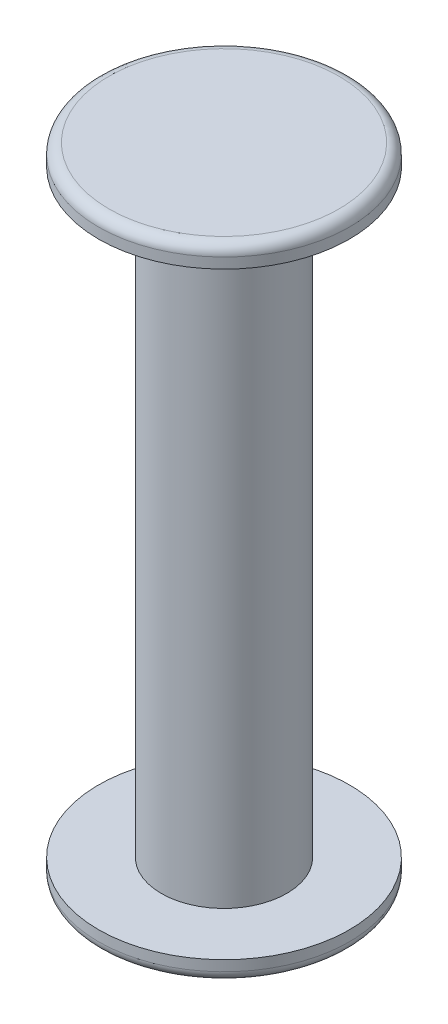
SolidWorks part; units mm, degrees
ref_plane "前视基准面" through (0, 0, 0) normal (0, 0, 1) x (1, 0, 0)
ref_plane "上视基准面" through (0, 0, 0) normal (0, 1, 0) x (1, 0, 0)
ref_plane "右视基准面" through (0, 0, 0) normal (1, 0, 0) x (0, 0, -1)
sketch "草图1" plane through (0, 0, 0) normal (0, 1, 0) x (1, 0, 0)
  circle A0 centre (0, 0) radius 3
  dimension "D1" = 6
extrude "凸台-拉伸1" add sketch "草图1" along normal mid plane 28.6
sketch "草图2" plane through (0, 14.3, 0) normal (0, 1, 0) x (1, 0, 0)
  circle A0 centre (0, 0) radius 6
  dimension "D1" = 12
extrude "凸台-拉伸2" add sketch "草图2" along normal blind 1
fillet "圆角1" radius 0.5 1 edges at (0, 15.3, 6)
mirror "镜向1" about plane through (0, 0, 0) normal (0, 1, 0) of "圆角1", "凸台-拉伸2"
